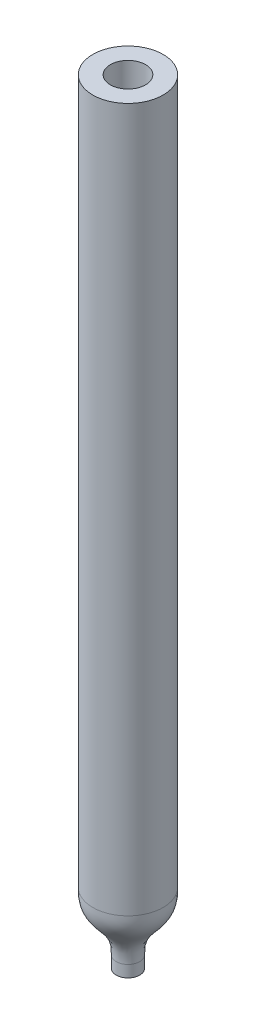
SolidWorks part; units mm, degrees
material "Glass"
ref_plane "Front Plane" through (0, 0, 0) normal (0, 0, 1) x (1, 0, 0)
ref_plane "Top Plane" through (0, 0, 0) normal (0, 1, 0) x (1, 0, 0)
ref_plane "Right Plane" through (0, 0, 0) normal (1, 0, 0) x (0, 0, -1)
sketch "Sketch1" plane through (0, 0, 0) normal (0, 0, 1) x (1, 0, 0)
  line L0 (1.5, 0) -> (0, 0) construction
  line L1 (1.5, 61) -> (3, 61)
  line L2 (1.5, 61) -> (1.5, 0)
  line L3 (0.25, -4) -> (1, -4) construction
  line L4 (3, 61) -> (3, 1)
  line L5 (0, 0) -> (0, -17.1222) construction
  line L6 (3, 1) -> (1.5, 1) construction
  line L8 (0.25, -4) -> (0.25, -5)
  line L9 (0.25, -5) -> (1, -5)
  line L10 (1, -4) -> (1, -5)
  spline S0 degree 5 poles (0.25, -4) (0.25, -2.8701) (0.25, -1.7403) (1.5, -2.2597) (1.5, -1.1299) (1.5, 0) knots 0 0 0 0 0 0 1 1 1 1 1 1
  spline S1 degree 5 poles (1, -4) (1, -2.8523) (1, -1.7047) (3, -1.2953) (3, -0.1477) (3, 1) knots 0 0 0 0 0 0 1 1 1 1 1 1
  dimension "D1" = 6
  dimension "D2" = 3
  dimension "D3" = 60
  dimension "D4" = 5
  dimension "D5" = 4
  dimension "D6" = 0.5
  dimension "D7" = 2
  dimension "D8" = 1
revolve "Revolve1" add sketch "Sketch1" angle 360 about L5
